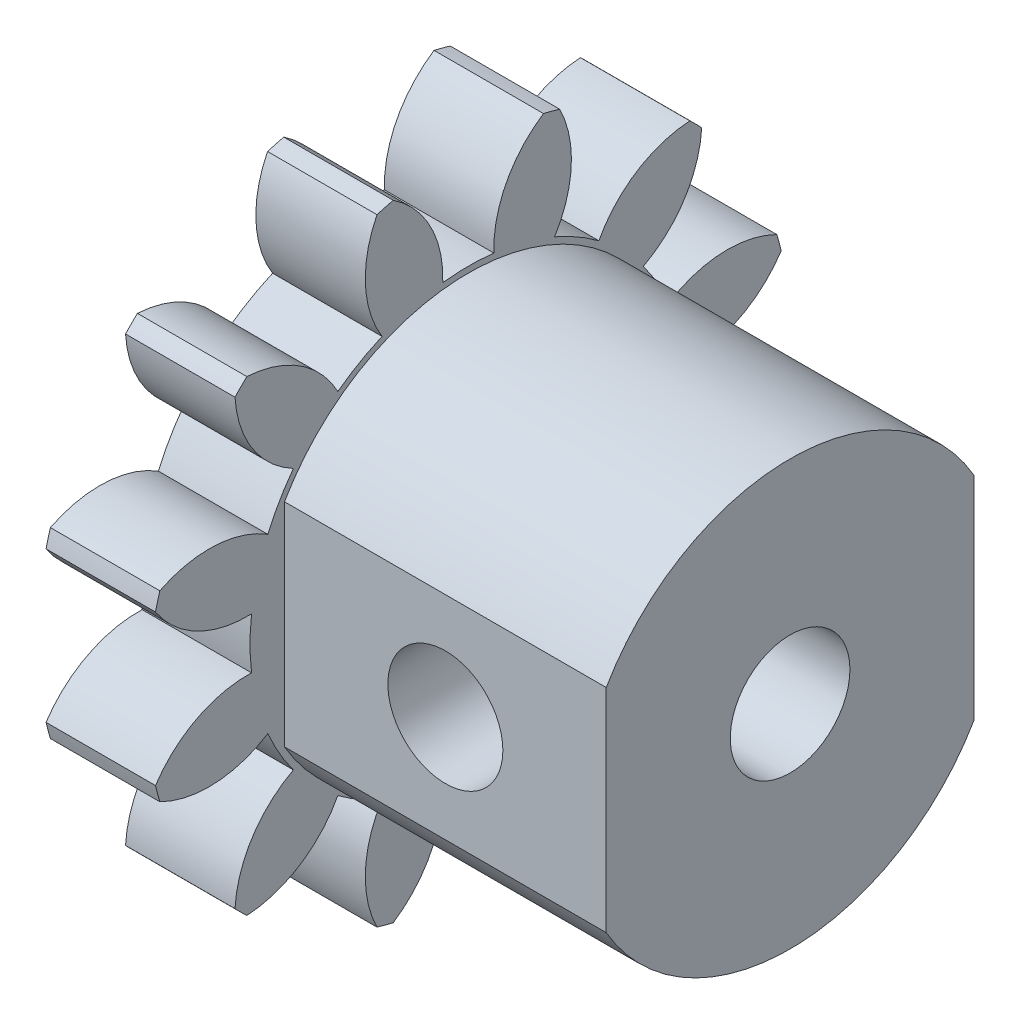
SolidWorks part; units mm, degrees
ref_plane "Plane1" through (0, 0, 0) normal (0, 0, 1) x (1, 0, 0)
ref_plane "Plane2" through (0, 0, 0) normal (0, 1, 0) x (1, 0, 0)
ref_plane "Plane3" through (0, 0, 0) normal (1, 0, 0) x (0, 0, -1)
sketch "HoldingSke" plane through (0, 0, 0) normal (0, 1, 0) x (1, 0, 0)
  line L0 (0, 0) -> (0.4891, -0.104)
  line L1 (-15, 0) -> (100, 0) construction
  line L2 (0, 0) -> (-2.1039, 2.3779)
  line L3 (0, 0) -> (-11.863, 4.5341)
  line L4 (0, 0) -> (8.4473, 1.7955)
  line L5 (0, 0) -> (-46.8476, -17.4728)
  line L6 (0, 0) -> (-3.9479, -2.6637)
  line L7 (-2.1039, 2.3779) -> (8.6586, 51.2059)
  line L8 (-76.2, 54.61) -> (-74.4, 54.61)
  line L9 (-71.009, 38.7566) -> (-53.1078, 45.2721)
  line L10 (-76.2, 71.12) -> (104.1128, 71.12)
  line L11 (0, 0) -> (-4.7625, 0)
  line L12 (-76.2, 101.6) -> (-76.133, 101.6)
  line L13 (24.9733, 27.94) -> (52.9518, 28.4284)
  line L14 (24.9733, 27.94) -> (24.9743, 27.94)
  line L15 (24.9733, 27.94) -> (100.4006, 29.5858)
  line L16 (-63.627, -2) -> (-12.827, -2)
  circle A0 centre (0, 0) radius 5
  circle A1 centre (0, 0) radius 9.499
  circle A2 centre (0, 0) radius 37.5
  circle A3 centre (0, 0) radius 5
  dimension "MHD" = 18.998
  dimension "Hub_dia" = 75
  dimension "Bore" = 10
  dimension "MBD" = 10
  dimension "Num_teeth" = 12
  dimension "Pitch" = 0.5
  dimension "Overall_len" = 50
  dimension "Show_teeth" = 12
  dimension "Thickness" = 4.7625
  dimension "OAL" = 50.0001
  dimension "T_dim" = 1.8
  dimension "Ap" = 20
  dimension "H" = 19.05
  dimension "Pitch_radius" = 180.3128
  dimension "Width" = 4.7625
  dimension "Backlash" = 0.067
  dimension "Addendum_fac" = 1
  dimension "Dedendum_fac" = 1.25
  dimension "Clearance_fac" = 0.25
  dimension "Dedendum_add" = 0.001
  dimension "Module" = 2
sketch "BasProSke" plane through (0, 0, 0) normal (0, 1, 0) x (1, 0, 0)
  line L0 (-10, 0) -> (60, 0) construction
  line L1 (0, 0) -> (0, 14)
  line L2 (0, 0) -> (4.7625, 0)
  line L3 (4.7625, 0) -> (4.7625, 14)
  line L4 (4.7625, 14) -> (0, 14)
  dimension "Thickness" = 4.7625
  dimension "Diameter" = 28
revolve "Base-Revolve" add sketch "BasProSke" angle 360 about L0
sketch "TooCutSke" plane through (0, 0, 0) normal (1, 0, 0) x (0, 0, -1)
  line L1 (0, 0) -> (0, 107) construction
  line L2 (0, 0) -> (-1.6834, 11.8813) construction
  line L3 (0, 0) -> (-6.1662, 23.0126) construction
  line L4 (-1.6834, 11.8813) -> (-3.0831, 11.5063) construction
  arc A0 (1.1119, 9.4337) -> (-1.1119, 9.4337) centre (0, 0) ccw
  arc A1 (3.2981, 13.6321) -> (-3.2981, 13.6321) centre (0, 0) ccw
  circle A2 centre (0, 0) radius 12 construction
  circle A3 centre (0, 0) radius 11.2763 construction
  arc A4 (-1.1119, 9.4337) -> (-3.2981, 13.6321) centre (-5.9089, 9.6042) ccw
  arc A5 (3.2981, 13.6321) -> (1.1119, 9.4337) centre (5.9089, 9.6042) ccw
  dimension "Root_dia" = 18.998
  dimension "Overcut_dia" = 28.0508
  dimension "Pitch_dia" = 24
  dimension "Base_dia" = 22.5526
  dimension "Flank_rad" = 4.8
  dimension "Half_ang" = 15
  dimension "Half_CT" = 1.4491
extrude "ToothCut" cut sketch "TooCutSke" along normal through all
fillet "Breaks" [suppressed] radius 0.04
fillet "RootFillets" [suppressed] radius 0.501
pattern_circular "TeethCuts" count 12 every 30 about axis through (-10, 0, 0) along (1, 0, 0) of "ToothCut", "RootFillets", "Breaks"
sketch "HubNeaOneSke" plane through (0, 0, 0) normal (-1, 0, 0) x (0, 0, 1)
  circle A0 centre (0, 0) radius 9.499
  dimension "Diameter" = 18.998
extrude "HubNearOne" [suppressed] add sketch "HubNeaOneSke" along normal blind 45.2376
sketch "HubNeaBotSke" plane through (0, 0, 0) normal (-1, 0, 0) x (0, 0, 1)
  circle A0 centre (0, 0) radius 9.499
  dimension "Diameter" = 18.998
extrude "HubNearBoth" [suppressed] add sketch "HubNeaBotSke" along normal blind 22.6188
ref_plane "FarPln" through (4.7625, 0, 0) normal (1, 0, 0) x (0, 0, -1)
sketch "HubFarSke" plane through (4.7625, 0, 0) normal (1, 0, 0) x (0, 0, -1)
  circle A0 centre (0, 0) radius 9.499
  dimension "Diameter" = 18.998
extrude "HubFar" [suppressed] add sketch "HubFarSke" along normal blind 22.6188
sketch "BorSke" plane through (0, 0, 0) normal (1, 0, 0) x (0, 0, -1)
  circle A0 centre (0, 0) radius 2.6035
  dimension "Diameter" = 5.207
extrude "Bore" cut sketch "BorSke" along normal mid plane 100.0001
sketch "KeySke" plane through (0, 0, 0) normal (1, 0, 0) x (0, 0, -1)
  line L0 (-2, 0) -> (-2, 6.8)
  line L1 (-2, 6.8) -> (2, 6.8)
  line L2 (2, 6.8) -> (2, 0)
  line L3 (0, 0) -> (0, 34) construction
  line L4 (-2, 0) -> (2, 0)
  dimension "Offset" = 6.8
  dimension "Width" = 4
extrude "Keyway" [suppressed] cut sketch "KeySke" along normal mid plane 100.0001
pattern_circular "Keyway2" [suppressed] count 2 every 90 about axis through (-10, 0, 0) along (1, 0, 0)
sketch "Sketch1" plane through (4.7625, 0, 0) normal (1, 0, 0) x (0, 0, -1)
  line L0 (0, 0) -> (14.605, 0) construction
  line L2 (-8, 4.6188) -> (-8, -4.6188)
  line L5 (8, -4.6188) -> (8, 4.6188)
  line L8 (0, -9.2376) -> (4, -6.9282) [skipped]
  line L9 (-8, -4.6188) -> (-4, -6.9282) [skipped]
  line L10 (4, 6.9282) -> (0, 9.2376) [skipped]
  line L11 (-4, 6.9282) -> (-8, 4.6188) [skipped]
  circle A0 centre (0, 0) radius 8 construction
  arc A1 (-8, 4.6188) -> (8, 4.6188) centre (0, 0) cw
  arc A4 (-8, -4.6188) -> (8, -4.6188) centre (0, 0) ccw
extrude "Boss-Extrude1" add sketch "Sketch1" along normal blind 14
sketch "Sketch2" plane through (18.7625, 0, 0) normal (1, 0, 0) x (0, 0, -1)
  circle A0 centre (0, 0) radius 2.6035 construction
  circle A1 centre (0, 0) radius 2.6035
extrude "Cut-Extrude1" cut sketch "Sketch2" against normal through all
sketch "Sketch3" plane through (0, 0, 8) normal (0, 0, 1) x (1, 0, 0)
  line L0 (18.7625, 0) -> (4.7625, 0) construction
  line L3 (18.7625, 4.6188) -> (18.7625, -4.6188) construction
  line L4 (4.7625, -1.1119) -> (4.7625, 1.1119) construction
  circle A0 centre (11.7625, 0) radius 2.5019
  dimension "D1" = 5.0038
extrude "Cut-Extrude2" cut sketch "Sketch3" against normal through all
equation "' \"Module@HoldingSke\" = 6.35"
equation "' \"Num_teeth@HoldingSke\" = 12"
equation "' \"Ap@HoldingSke\" =  20"
equation "' \"Ap@HoldingSke\" = 20"
equation "' \"Width@HoldingSke\" = 0.5 * 25.4"
equation "' \"Hub_dia@HoldingSke\"= 1 * 25.4"
equation "' \"Hub_dia@HoldingSke\" = 1 * 25.4"
equation "' \"Overall_len@HoldingSke\" = 1.0 * 25.4"
equation "' \"Bore@HoldingSke\" = 0.75 * 25.4"
equation "' \"T_dim@HoldingSke\" = 0.1 * 25.4"
equation "' \"Width@KeySke\" = 0.25 * 25.4"
equation "' \"Show_teeth@HoldingSke\" = 13"
equation "' \"Backlash@HoldingSke\" = 0.009 * 25.4"
equation "' \"Addendum_fac@HoldingSke\" = 1.0"
equation "' \"Dedendum_fac@HoldingSke\" = 1.25"
equation "' \"Dedendum_add@HoldingSke\" = 0.00005 * 25.4"
equation "' \"Clearance_fac@HoldingSke\" = 0.25"
equation "\"Pitch@HoldingSke\" = 1 / \"Module@HoldingSke\""
equation "\"Overcut_dia@TooCutSke\" = (\"Num_teeth@HoldingSke\" + 2 * \"Addendum_fac@HoldingSke\") / \"Pitch@HoldingSke\" + 0.002 * 25.4"
equation "\"Pitch_dia@TooCutSke\" = \"Num_teeth@HoldingSke\" / \"Pitch@HoldingSke\""
equation "\"Base_dia@TooCutSke\" = \"Num_teeth@HoldingSke\" / \"Pitch@HoldingSke\" * cos((\"Ap@HoldingSke\"  * 3.14159265 / 180))"
equation "\"Root_dia@TooCutSke\" = (\"Num_teeth@HoldingSke\" + 2) / \"Pitch@HoldingSke\" - 2 * (\"Addendum_fac@HoldingSke\" + \"Dedendum_fac@HoldingSke\") / \"Pitch@HoldingSke\" - \"Dedendum_add@HoldingSke\" * 2"
equation "\"Half_ang@TooCutSke\" = 180 / \"Num_teeth@HoldingSke\""
equation "\"Half_CT@TooCutSke\" = \"Num_teeth@HoldingSke\" / \"Pitch@HoldingSke\" * sin((3.14159265 / 2 / \"Num_teeth@HoldingSke\")) / 2 - 7 * \"Backlash@HoldingSke\" / 4"
equation "\"Flank_rad@TooCutSke\" = \"Num_teeth@HoldingSke\" / \"Pitch@HoldingSke\" / 5"
equation "\"Radius@RootFillets\" = \"Clearance_fac@HoldingSke\" / \"Pitch@HoldingSke\" + \"Dedendum_add@HoldingSke\""
equation "\"Break_rad@Breaks\" = 0.02 / \"Pitch@HoldingSke\""
equation "\"Thickness@HoldingSke\" = \"Width@HoldingSke\""
equation "\"OAL@HoldingSke\" = \"Thickness@HoldingSke\""
equation "\"MHD@HoldingSke\" = (\"Num_teeth@HoldingSke\" + 2) / \"Pitch@HoldingSke\" - 2 * (\"Addendum_fac@HoldingSke\" + \"Dedendum_fac@HoldingSke\")  / \"Pitch@HoldingSke\" - \"Dedendum_add@HoldingSke\" * 2"
equation "\"MBD@HoldingSke\" = (\"Num_teeth@HoldingSke\" + 2) / \"Pitch@HoldingSke\" - 2 * (\"Addendum_fac@HoldingSke\" + \"Dedendum_fac@HoldingSke\")  / \"Pitch@HoldingSke\" - \"Dedendum_add@HoldingSke\" * 2 - 0.002 * 25.4"
equation "\"MHD@HoldingSke\" = ((sgn( \"MHD@HoldingSke\" - \"Hub_dia@HoldingSke\" )-1)*( \"MHD@HoldingSke\" - \"Hub_dia@HoldingSke\" ))/-2+ \"Hub_dia@HoldingSke\""
equation "\"MBD@HoldingSke\" = ((sgn( \"MBD@HoldingSke\" - \"Bore@HoldingSke\" )-1)*( \"MBD@HoldingSke\" - \"Bore@HoldingSke\" ))/-2+ \"Bore@HoldingSke\""
equation "\"OAL@HoldingSke\" = ((sgn( \"OAL@HoldingSke\" - \"Overall_len@HoldingSke\" )+1)*( \"OAL@HoldingSke\" - \"Overall_len@HoldingSke\" ))/2 + \"Overall_len@HoldingSke\" + 0.000002 * 25.4"
equation "\"Num_teeth@TeethCuts\" = int( \"Show_teeth@HoldingSke\" ) + 1"
equation "\"Num_teeth@TeethCuts\" = ((sgn( \"Num_teeth@TeethCuts\" - \"Num_teeth@HoldingSke\" )-1)*( \"Num_teeth@TeethCuts\" - \"Num_teeth@HoldingSke\" ))/-2+ \"Num_teeth@HoldingSke\""
equation "\"Num_teeth@TeethCuts\" = ((sgn( \"Num_teeth@TeethCuts\" - 2.0)+1)*( \"Num_teeth@TeethCuts\" - 2.0))/2 +2.0"
equation "\"Angle@TeethCuts\" = 360.0 / \"Num_teeth@HoldingSke\""
equation "\"Diameter@BasProSke\" = (\"Num_teeth@HoldingSke\" + 2 * \"Addendum_fac@HoldingSke\") / \"Pitch@HoldingSke\""
equation "\"Thickness@BasProSke\"  = \"Thickness@HoldingSke\""
equation "' \"Fillet_rad@BasProSke\" =  \"Thickness@HoldingSke\" * 0.05"
equation "' \"Fillet_rad@BasProSke\" = \"Thickness@HoldingSke\" * 0.05"
equation "\"MHD@HoldingSke\" = ((sgn( \"MHD@HoldingSke\" - \"Root_dia@TooCutSke\" )-1)*( \"MHD@HoldingSke\" - \"Root_dia@TooCutSke\" ))/-2+ \"Root_dia@TooCutSke\""
equation "\"Diameter@HubNeaOneSke\" = \"MHD@HoldingSke\""
equation "\"Length@HubNearOne\" = \"OAL@HoldingSke\" - \"Thickness@BasProSke\""
equation "\"Diameter@HubNeaBotSke\" = \"MHD@HoldingSke\""
equation "\"Length@HubNearBoth\" = ( \"OAL@HoldingSke\" - \"Thickness@BasProSke\" ) / 2.0"
equation "\"Thickness@FarPln\" = \"Thickness@BasProSke\""
equation "\"Diameter@HubFarSke\" = \"MHD@HoldingSke\""
equation "\"Length@HubFar\" = ( \"OAL@HoldingSke\" - \"Thickness@BasProSke\" ) / 2.0"
equation "\"D1@Bore\" = \"OAL@HoldingSke\" * 2.0"
equation "\"D1@Keyway\" = \"OAL@HoldingSke\" * 2.0"
equation "\"Offset@KeySke\" = \"T_dim@HoldingSke\" + \"MBD@HoldingSke\" / 2.0"
